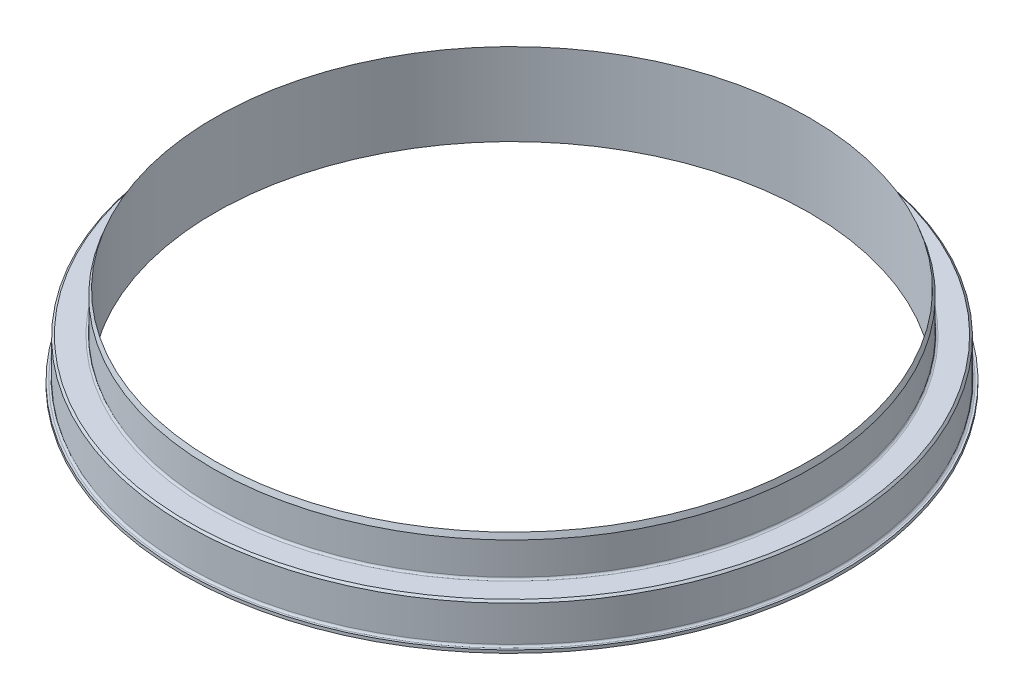
SolidWorks part; units mm, degrees
ref_plane "Front Plane" through (0, 0, 0) normal (0, 0, 1) x (1, 0, 0)
ref_plane "Top Plane" through (0, 0, 0) normal (0, 1, 0) x (1, 0, 0)
ref_plane "Right Plane" through (0, 0, 0) normal (1, 0, 0) x (0, 0, -1)
sketch "Sketch1" plane through (0, 0, 0) normal (0, 0, 1) x (1, 0, 0)
  line L0 (0, 28.739) -> (0, -28.739) construction
  line L1 (0, -55) -> (0, 55) construction
  line L2 (76.2, 28.739) -> (76.2, -28.739) construction
  line L3 (84.455, 28.739) -> (84.455, -28.739) construction
  line L4 (0, 0) -> (84.455, 0) construction
  line L5 (76.2, 21.082) -> (76.2, 0)
  line L6 (76.2, 0) -> (84.455, 0)
  line L7 (83.439, 10.922) -> (83.439, 0.762)
  line L8 (83.439, 10.922) -> (76.708, 10.922)
  line L9 (76.708, 10.922) -> (76.708, 19.6863)
  line L10 (83.439, 0.762) -> (84.455, 0.762)
  line L11 (76.2, 21.082) -> (76.708, 19.6863)
  line L12 (84.455, 0.762) -> (84.455, 0)
  dimension "D1" = 76.2
  dimension "D2" = 84.455
  dimension "D3" = 0.508
  dimension "D5" = 10.16
  dimension "D4" = 6.731
  dimension "D7" = 10.16
  dimension "D8" = 0.762
  dimension "D9" = 1.016
  dimension "D6" = 20
revolve "Revolve1" add sketch "Sketch1" angle 360 about L0
fillet "Fillet1" radius 0.508 2 edges at (0, 10.922, 76.708) (0, 0.762, 83.439)
chamfer "Chamfer1" distance 0.508 angle 45 1 edges at (0, 10.922, 83.439)
equation "\"Di\"= 6.0in"
equation "\"Do\"= 6.65in"
equation "\"Ri\"= \"Di\" / 2"
equation "\"Ro\"= \"Do\" / 2"
equation "\"D1@Sketch1\"=\"Ri\""
equation "\"D2@Sketch1\"=\"Ro\""
